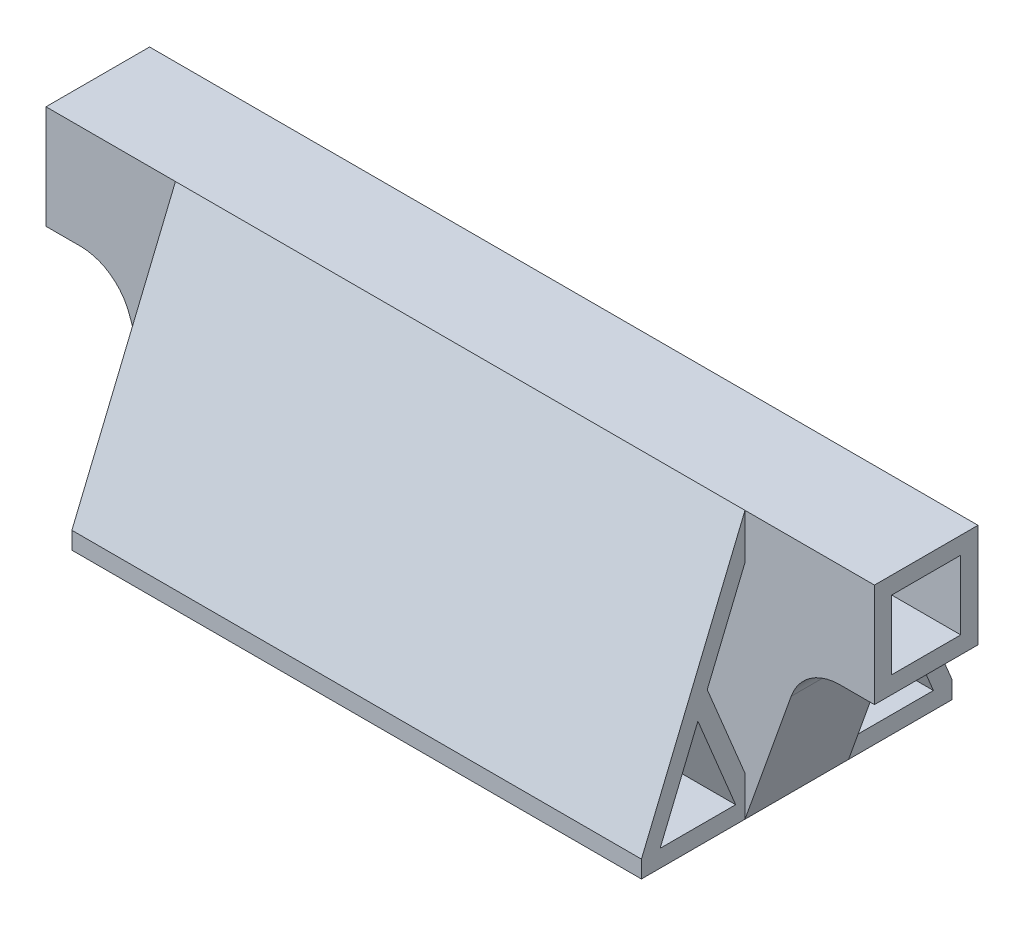
SolidWorks part; units mm, degrees
ref_plane "Front" through (0, 0, 0) normal (0, 0, 1) x (1, 0, 0)
ref_plane "Top" through (0, 0, 0) normal (0, 1, 0) x (1, 0, 0)
ref_plane "Right" through (0, 0, 0) normal (1, 0, 0) x (0, 0, -1)
sketch "Sketch1" plane through (0, 0, 0) normal (0, 0, 1) x (1, 0, 0)
  line L0 (-52.3875, 0) -> (52.3875, 0)
  line L1 (-52.3875, 0) -> (-52.3875, 30.1625) construction
  line L2 (52.3875, 0) -> (52.3875, 30.1625) construction
  line L3 (-52.3875, 30.1625) -> (52.3875, 30.1625) construction
  line L4 (-52.3875, 30.1625) -> (-76.2, 30.1625) construction
  line L5 (-76.2, 30.1625) -> (-76.2, 49.2125)
  line L6 (-76.2, 49.2125) -> (76.2, 49.2125)
  line L7 (76.2, 49.2125) -> (76.2, 30.1625)
  line L8 (76.2, 30.1625) -> (52.3875, 30.1625) construction
  line L9 (0, 0) -> (0, 49.2125) construction
  line L10 (-69.85, 20.6375) -> (69.85, 20.6375) construction
  line L11 (-52.3875, 0) -> (-60.8773, 23.8337)
  line L12 (-69.85, 30.1625) -> (-76.2, 30.1625)
  line L13 (52.3875, 0) -> (60.8773, 23.8337)
  line L14 (69.85, 30.1625) -> (76.2, 30.1625)
  circle A0 centre (-69.85, 20.6375) radius 9.525 construction
  circle A1 centre (69.85, 20.6375) radius 9.525 construction
  arc A2 (-60.8773, 23.8337) -> (-69.85, 30.1625) centre (-69.85, 20.6375) ccw
  arc A3 (60.8773, 23.8337) -> (69.85, 30.1625) centre (69.85, 20.6375) cw
  point P15 (0, 20.6375)
  dimension "D6" = 19.05
  dimension "D1" = 104.775
  dimension "D2" = 30.1625
  dimension "D3" = 152.4
  dimension "D4" = 19.05
  dimension "D5" = 17.4625
extrude "Boss-Extrude1" add sketch "Sketch1" along normal mid plane 57.15
sketch "Sketch11" plane through (0, 0, 0) normal (1, 0, 0) x (0, 0, -1)
  line L0 (-28.575, 0) -> (-28.575, 3.175) construction
  line L1 (-28.575, 0) -> (-28.575, 23.8337) construction
  line L2 (-28.575, 3.175) -> (28.575, 3.175) construction
  line L3 (28.575, 0) -> (28.575, 23.8337) construction
  line L4 (28.575, 3.175) -> (28.575, 0) construction
  line L5 (-9.525, 49.2125) -> (-9.525, 30.1625) construction
  line L6 (-28.575, 49.2125) -> (28.575, 49.2125) construction
  line L7 (-9.525, 30.1625) -> (9.525, 30.1625) construction
  line L8 (9.525, 30.1625) -> (9.525, 49.2125) construction
  line L9 (9.525, 49.2125) -> (-9.525, 49.2125) construction
  line L10 (0, 0) -> (0, 30.1625) construction
  line L11 (-28.575, 0) -> (28.575, 0) construction
  line L12 (-9.525, 30.1625) -> (-28.575, 3.175)
  line L13 (-28.575, 3.175) -> (-28.575, 49.2125)
  line L14 (-28.575, 49.2125) -> (-9.525, 49.2125)
  line L15 (-9.525, 49.2125) -> (-9.525, 30.1625)
  line L16 (28.575, 3.175) -> (9.525, 30.1625)
  line L17 (9.525, 30.1625) -> (9.525, 49.2125)
  line L18 (9.525, 49.2125) -> (28.575, 49.2125)
  line L19 (28.575, 49.2125) -> (28.575, 3.175)
  line L20 (0, 46.0375) -> (0, 49.2125) construction
  line L21 (-6.35, 33.3375) -> (6.35, 33.3375)
  line L22 (-6.35, 33.3375) -> (-6.35, 46.0375)
  line L23 (-6.35, 46.0375) -> (6.35, 46.0375)
  line L24 (6.35, 33.3375) -> (6.35, 46.0375)
  line L25 (-6.35, 33.3375) -> (6.35, 46.0375) construction
  line L26 (-6.35, 46.0375) -> (6.35, 33.3375) construction
  line L27 (6.35, 39.6875) -> (9.525, 39.6875) construction
  line L28 (-6.35, 39.6875) -> (-9.525, 39.6875) construction
  line L29 (0, 33.3375) -> (0, 30.1625) construction
  line L30 (-9.525, 30.1625) -> (-9.525, 3.175) construction
  line L31 (9.525, 30.1625) -> (9.525, 3.175) construction
  line L32 (-24.6887, 3.175) -> (-12.7, 20.159)
  line L33 (-12.7, 20.159) -> (-12.7, 3.175)
  line L34 (-12.7, 3.175) -> (-24.6887, 3.175)
  line L36 (-12.7, 11.667) -> (-9.525, 11.667) construction
  line L37 (-18.6943, 11.667) -> (-21.2882, 13.4979) construction
  line L38 (24.6887, 3.175) -> (12.7, 3.175)
  line L39 (12.7, 3.175) -> (12.7, 20.159)
  line L40 (12.7, 20.159) -> (24.6887, 3.175)
  line L41 (18.6943, 11.667) -> (21.2882, 13.4979) construction
  line L43 (12.7, 11.667) -> (9.525, 11.667) construction
  point P23 (0, 39.6875)
  point P40 (13.3372, 18.1514)
  dimension "D1" = 19.05
  dimension "D2" = 3.175
  dimension "D3" = 12.7
extrude "Cut-Extrude8" [suppressed] cut sketch "Sketch11" against normal through all both and the other way through all
sketch "Sketch2" plane through (0, 0, 0) normal (0, 0, 1) x (1, 0, 0)
  line L8 (-69.85, 33.3375) -> (69.85, 33.3375)
  line L9 (-61.4497, 30.1625) -> (-1.5875, 30.1625)
  line L11 (69.85, 30.1625) -> (76.2, 30.1625) construction
  line L12 (0, 30.1625) -> (0, 33.3375) construction
  line L13 (0, 30.1625) -> (0, 3.175) construction
  line L14 (1.5875, 3.175) -> (1.5875, 30.1625)
  line L15 (-1.5875, 30.1625) -> (-1.5875, 3.175)
  line L16 (-57.8863, 24.8991) -> (-50.148, 3.175)
  line L17 (-50.148, 3.175) -> (50.148, 3.175)
  line L18 (-57.8863, 24.8991) -> (-50.148, 3.175)
  line L19 (50.148, 3.175) -> (57.8863, 24.8991)
  line L20 (73.025, 33.3375) -> (73.025, 46.0375)
  line L21 (73.025, 46.0375) -> (-73.025, 46.0375)
  line L22 (-73.025, 46.0375) -> (-73.025, 33.3375)
  line L23 (50.148, 3.175) -> (57.8863, 24.8991)
  line L25 (-50.148, 3.175) -> (-1.5875, 3.175)
  line L28 (73.025, 33.3375) -> (73.025, 46.0375)
  line L29 (73.025, 46.0375) -> (-73.025, 46.0375)
  line L30 (-73.025, 46.0375) -> (-73.025, 33.3375)
  line L32 (1.5875, 16.6687) -> (-1.5875, 16.6687) construction
  line L33 (0, 3.175) -> (0, 0) construction
  line L34 (1.5875, 3.175) -> (50.148, 3.175)
  line L35 (69.85, 33.3375) -> (73.025, 33.3375)
  line L36 (69.85, 33.3375) -> (73.025, 33.3375)
  line L37 (-73.025, 33.3375) -> (-69.85, 33.3375)
  line L38 (-73.025, 33.3375) -> (-69.85, 33.3375)
  line L39 (1.5875, 30.1625) -> (61.4497, 30.1625)
  line L40 (1.5875, 30.1625) -> (0, 30.1625) construction
  line L41 (0, 30.1625) -> (-1.5875, 30.1625) construction
  line L42 (1.5875, 3.175) -> (0, 3.175) construction
  line L43 (0, 3.175) -> (-1.5875, 3.175) construction
  arc A2 (69.85, 33.3375) -> (57.8863, 24.8991) centre (69.85, 20.6375) ccw
  arc A3 (61.4497, 30.1625) -> (57.8863, 24.8991) centre (69.85, 20.6375) ccw
  arc A4 (-57.8863, 24.8991) -> (-69.85, 33.3375) centre (-69.85, 20.6375) ccw
  arc A5 (-57.8863, 24.8991) -> (-61.4497, 30.1625) centre (-69.85, 20.6375) ccw
  dimension "D1" = 3.175
extrude "Cut-Extrude1" cut sketch "Sketch2" along normal offset from surface 22.225 and the other way offset from surface (6.35 mm away) 22.225 up to face at (0, 26.9588, 28.575) other way up to face at (0, 26.9588, -28.575)
sketch "Sketch3" plane through (0, 0, 0) normal (1, 0, 0) x (0, 0, -1)
  line L0 (0, 0) -> (0, 39.6875) construction
  line L1 (-6.35, 33.3375) -> (6.35, 33.3375)
  line L2 (-6.35, 33.3375) -> (-6.35, 46.0375)
  line L3 (-6.35, 46.0375) -> (6.35, 46.0375)
  line L4 (6.35, 33.3375) -> (6.35, 46.0375)
  line L5 (-6.35, 33.3375) -> (6.35, 46.0375) construction
  line L6 (-6.35, 46.0375) -> (6.35, 33.3375) construction
  line L7 (-28.575, 0) -> (28.575, 0) construction
  line L8 (0, 39.6875) -> (28.575, 39.6875) construction
  line L9 (28.575, 30.1625) -> (28.575, 49.2125) construction
  point P0 (0, 39.6875)
  dimension "D1" = 12.7
extrude "Cut-Extrude2" cut sketch "Sketch3" against normal through all both and the other way through all
sketch "Sketch6" plane through (0, 0, 0) normal (1, 0, 0) x (0, 0, -1)
  line L1 (28.575, 49.2125) -> (9.525, 49.2125)
  line L2 (-28.575, 49.2125) -> (28.575, 49.2125) construction
  line L4 (-9.525, 49.2125) -> (-9.525, 30.1625) construction
  line L5 (-28.575, 30.1625) -> (28.575, 30.1625) construction
  line L6 (-9.525, 30.1625) -> (9.525, 30.1625) construction
  line L7 (9.525, 30.1625) -> (9.525, 49.2125) construction
  line L8 (9.525, 49.2125) -> (-9.525, 49.2125) construction
  line L9 (6.35, 39.6875) -> (9.525, 39.6875) construction
  line L10 (6.35, 33.3375) -> (6.35, 46.0375) construction
  line L11 (-9.525, 39.6875) -> (-6.35, 39.6875) construction
  line L12 (-6.35, 46.0375) -> (-6.35, 33.3375) construction
  line L13 (9.525, 30.1625) -> (9.525, 7.3269) construction
  line L14 (-28.575, 0) -> (28.575, 0) construction
  line L15 (11.243, 3.175) -> (28.575, 3.175) construction
  line L16 (-9.525, 30.1625) -> (-9.525, 7.3269) construction
  line L17 (9.525, 3.175) -> (-9.525, 3.175) construction
  line L18 (-11.243, 3.175) -> (-28.575, 3.175) construction
  line L19 (-28.575, 0) -> (-28.575, 23.8337) construction
  line L20 (0, 3.175) -> (0, 0) construction
  line L21 (9.525, 40.9086) -> (9.525, 7.3269)
  line L22 (11.243, 3.175) -> (25.1389, 3.175)
  line L23 (25.1389, 3.175) -> (18.191, 19.9658)
  line L24 (17.332, 22.0418) -> (20.2657, 23.2558) construction
  line L25 (-9.525, 49.2125) -> (-28.575, 3.175)
  line L26 (-28.575, 3.175) -> (-28.575, 49.2125)
  line L27 (-28.575, 49.2125) -> (-9.525, 49.2125)
  line L28 (-25.1389, 3.175) -> (-11.243, 3.175)
  line L29 (-9.525, 7.3269) -> (-9.525, 40.9086)
  line L30 (-9.525, 40.9086) -> (-16.4729, 24.1178)
  line L31 (-17.332, 22.0418) -> (-20.2657, 23.2558) construction
  line L32 (-9.525, 3.175) -> (-17.332, 22.0418) construction
  line L33 (9.525, 3.175) -> (17.332, 22.0418) construction
  line L34 (-9.525, 7.3269) -> (-16.4729, 24.1178)
  line L35 (-11.243, 3.175) -> (-18.191, 19.9658)
  line L36 (-14.717, 11.5704) -> (-11.7833, 12.7844) construction
  line L37 (9.525, 7.3269) -> (16.4729, 24.1178)
  line L38 (11.243, 3.175) -> (18.191, 19.9658)
  line L39 (14.717, 11.5704) -> (11.7833, 12.7844) construction
  line L40 (-18.191, 19.9658) -> (-25.1389, 3.175)
  line L41 (-9.525, 3.175) -> (-9.525, 0) construction
  line L42 (9.525, 3.175) -> (9.525, 0) construction
  line L43 (16.4729, 24.1178) -> (9.525, 40.9086)
  line L44 (-11.243, 3.175) -> (-9.525, 3.175) construction
  line L45 (-9.525, 3.175) -> (-9.525, 7.3269) construction
  line L46 (-18.191, 19.9658) -> (-17.332, 22.0418) construction
  line L47 (-17.332, 22.0418) -> (-16.4729, 24.1178) construction
  line L48 (9.525, 7.3269) -> (9.525, 3.175) construction
  line L49 (9.525, 3.175) -> (11.243, 3.175) construction
  line L50 (18.191, 19.9658) -> (17.332, 22.0418) construction
  line L51 (17.332, 22.0418) -> (16.4729, 24.1178) construction
  line L52 (28.575, 0) -> (28.575, 23.8337) construction
  line L53 (28.575, 3.175) -> (28.575, 49.2125)
  line L54 (9.525, 49.2125) -> (28.575, 3.175)
  dimension "D1" = 3.175
extrude "Cut-Extrude4" cut sketch "Sketch6" against normal through all both and the other way through all
sketch "Sketch8" plane through (0, 0, 0) normal (0, -1, 0) x (1, 0, 0)
  line L1 (52.3875, 28.575) -> (76.2, 28.575)
  line L2 (52.3875, 28.575) -> (52.3875, 9.525)
  line L3 (52.3875, 9.525) -> (76.2, 9.525)
  line L4 (76.2, 28.575) -> (76.2, 9.525)
  line L5 (52.3875, -28.575) -> (76.2, -28.575)
  line L6 (52.3875, -28.575) -> (52.3875, -9.525)
  line L7 (52.3875, -9.525) -> (76.2, -9.525)
  line L8 (76.2, -28.575) -> (76.2, -9.525)
  line L9 (-52.3875, 28.575) -> (-76.2, 28.575)
  line L10 (-52.3875, 28.575) -> (-52.3875, 9.525)
  line L11 (-52.3875, 9.525) -> (-76.2, 9.525)
  line L12 (-76.2, 28.575) -> (-76.2, 9.525)
  line L13 (-52.3875, -28.575) -> (-76.2, -28.575)
  line L14 (-52.3875, -28.575) -> (-52.3875, -9.525)
  line L15 (-52.3875, -9.525) -> (-76.2, -9.525)
  line L16 (-76.2, -28.575) -> (-76.2, -9.525)
extrude "Cut-Extrude5" cut sketch "Sketch8" against normal through all
sketch "Sketch9" plane through (0, 10.5597, -25.5193) normal (0, 0.3824, -0.924) x (-1, 0, 0)
  line L0 (0, -6.6782) -> (0, 11.4934) construction
  line L1 (0, 15.9868) -> (0, 34.1584) construction
  line L2 (-1.5875, -6.6782) -> (-1.5875, 11.4934) construction
  line L3 (-1.5875, 15.9868) -> (-1.5875, 34.1584) construction
  line L4 (-52.3875, 15.9868) -> (52.3875, 15.9868)
  line L5 (-52.3875, 34.1584) -> (-52.3875, 15.9868)
  line L6 (52.3875, 34.1584) -> (-52.3875, 34.1584)
  line L7 (-52.3875, 34.1584) -> (-52.3875, 15.9868) construction
  line L8 (-52.3875, 15.9868) -> (52.3875, 15.9868) construction
  line L10 (52.3875, 34.1584) -> (-52.3875, 34.1584) construction
  line L12 (-52.3875, -6.6782) -> (52.3875, -6.6782)
  line L13 (-52.3875, 11.4934) -> (-52.3875, -6.6782)
  line L14 (52.3875, 11.4934) -> (-52.3875, 11.4934)
  line L15 (-52.3875, 11.4934) -> (-52.3875, -6.6782) construction
  line L16 (-52.3875, -6.6782) -> (52.3875, -6.6782) construction
  line L18 (52.3875, 11.4934) -> (-52.3875, 11.4934) construction
  line L20 (1.5875, -6.6782) -> (1.5875, 11.4934) construction
  line L21 (1.5875, 15.9868) -> (1.5875, 34.1584) construction
  line L22 (-1.5875, 2.4076) -> (1.5875, 2.4076) construction
  line L23 (-1.5875, 25.0726) -> (1.5875, 25.0726) construction
  line L24 (-49.2125, 34.1584) -> (-49.2125, 15.9868) construction
  line L25 (-49.2125, 11.4934) -> (-49.2125, -6.6782) construction
  line L26 (49.2125, 34.1584) -> (49.2125, 15.9868) construction
  line L27 (49.2125, 11.4934) -> (49.2125, -6.6782) construction
  line L28 (49.2125, 2.4076) -> (52.3875, 2.4076) construction
  line L29 (49.2125, 25.0726) -> (52.3875, 25.0726) construction
  line L30 (-52.3875, 25.0726) -> (-49.2125, 25.0726) construction
  line L31 (-52.3875, 2.4076) -> (-49.2125, 2.4076) construction
  line L47 (-47.625, 9.9059) -> (-3.175, 9.9059) construction
  line L48 (-3.175, 9.9059) -> (-3.175, -5.0907) construction
  line L49 (-3.175, -5.0907) -> (-47.625, -5.0907) construction
  line L50 (-47.625, -5.0907) -> (-47.625, 9.9059) construction
  line L66 (-49.2125, 2.4076) -> (-47.625, 2.4076) construction
  line L67 (-3.175, 2.4076) -> (-1.5875, 2.4076) construction
  line L68 (-25.4, -5.0907) -> (-25.4, -6.6782) construction
  line L69 (-25.4, 9.9059) -> (-25.4, 11.4934) construction
  line L85 (-47.625, -5.0907) -> (-47.625, 3.8568)
  line L86 (-47.625, 3.8568) -> (-42.1077, -5.0907)
  line L87 (-42.1077, -5.0907) -> (-47.625, -5.0907)
  line L88 (-47.625, 9.9059) -> (-38.3776, -5.0907)
  line L104 (-38.3776, -5.0907) -> (-29.1301, 9.9059)
  line L105 (-29.1301, 9.9059) -> (-47.625, 9.9059)
  line L106 (-34.6474, -5.0907) -> (-25.4, 9.9059)
  line L107 (-25.4, 9.9059) -> (-16.1526, -5.0907)
  line L108 (52.3875, -7.9919) -> (52.3875, 41.8313) construction
  line L109 (-16.1526, -5.0907) -> (-34.6474, -5.0907)
  line L110 (-3.175, 9.9059) -> (-12.4224, -5.0907)
  line L111 (-12.4224, -5.0907) -> (-21.6699, 9.9059)
  line L112 (52.3875, -6.6782) -> (52.3875, 11.4934)
  line L113 (52.3875, -6.6782) -> (52.3875, 11.4934) construction
  line L114 (52.3875, 15.9868) -> (52.3875, 34.1584)
  line L115 (52.3875, 15.9868) -> (52.3875, 34.1584) construction
  line L116 (-21.6699, 9.9059) -> (-3.175, 9.9059)
  line L117 (-3.175, -5.0907) -> (-3.175, 3.8568)
  line L118 (-3.175, 3.8568) -> (-8.6923, -5.0907)
  line L119 (-8.6923, -5.0907) -> (-3.175, -5.0907)
  line L120 (-5.9337, -0.6169) -> (-8.6362, 1.0495) construction
  line L121 (-17.0462, 2.4076) -> (-19.7487, 0.7412) construction
  line L122 (-33.7538, 2.4076) -> (-31.0513, 0.7412) construction
  line L123 (-44.8663, -0.6169) -> (-42.1638, 1.0495) construction
  line L124 (47.625, 3.8568) -> (42.1077, -5.0907)
  line L125 (47.625, -5.0907) -> (47.625, 3.8568)
  line L126 (42.1077, -5.0907) -> (47.625, -5.0907)
  line L127 (38.3776, -5.0907) -> (29.1301, 9.9059)
  line L128 (47.625, 9.9059) -> (38.3776, -5.0907)
  line L129 (29.1301, 9.9059) -> (47.625, 9.9059)
  line L130 (25.4, 9.9059) -> (16.1526, -5.0907)
  line L131 (34.6474, -5.0907) -> (25.4, 9.9059)
  line L132 (16.1526, -5.0907) -> (34.6474, -5.0907)
  line L133 (12.4224, -5.0907) -> (21.6699, 9.9059)
  line L134 (3.175, 9.9059) -> (12.4224, -5.0907)
  line L135 (21.6699, 9.9059) -> (3.175, 9.9059)
  line L136 (3.175, 3.8568) -> (8.6923, -5.0907)
  line L137 (3.175, -5.0907) -> (3.175, 3.8568)
  line L138 (8.6923, -5.0907) -> (3.175, -5.0907)
  line L139 (-52.3875, 13.7401) -> (52.3875, 13.7401) construction
  line L140 (-52.3875, 41.8313) -> (-52.3875, -7.9919) construction
  line L141 (0, 11.4934) -> (0, 15.9868) construction
  line L142 (47.625, 32.5709) -> (47.625, 23.6234)
  line L143 (42.1077, 32.5709) -> (47.625, 32.5709)
  line L144 (47.625, 23.6234) -> (42.1077, 32.5709)
  line L145 (47.625, 17.5743) -> (38.3776, 32.5709)
  line L146 (29.1301, 17.5743) -> (47.625, 17.5743)
  line L147 (38.3776, 32.5709) -> (29.1301, 17.5743)
  line L148 (34.6474, 32.5709) -> (25.4, 17.5743)
  line L149 (16.1526, 32.5709) -> (34.6474, 32.5709)
  line L150 (25.4, 17.5743) -> (16.1526, 32.5709)
  line L151 (3.175, 17.5743) -> (12.4224, 32.5709)
  line L152 (21.6699, 17.5743) -> (3.175, 17.5743)
  line L153 (12.4224, 32.5709) -> (21.6699, 17.5743)
  line L154 (-3.175, 23.6234) -> (-8.6923, 32.5709)
  line L155 (-3.175, 32.5709) -> (-3.175, 23.6234)
  line L156 (-8.6923, 32.5709) -> (-3.175, 32.5709)
  line L157 (3.175, 32.5709) -> (3.175, 23.6234)
  line L158 (8.6923, 32.5709) -> (3.175, 32.5709)
  line L159 (3.175, 23.6234) -> (8.6923, 32.5709)
  line L160 (-12.4224, 32.5709) -> (-21.6699, 17.5743)
  line L161 (-3.175, 17.5743) -> (-12.4224, 32.5709)
  line L162 (-21.6699, 17.5743) -> (-3.175, 17.5743)
  line L163 (-25.4, 17.5743) -> (-16.1526, 32.5709)
  line L164 (-34.6474, 32.5709) -> (-25.4, 17.5743)
  line L165 (-16.1526, 32.5709) -> (-34.6474, 32.5709)
  line L166 (-38.3776, 32.5709) -> (-29.1301, 17.5743)
  line L167 (-47.625, 17.5743) -> (-38.3776, 32.5709)
  line L168 (-29.1301, 17.5743) -> (-47.625, 17.5743)
  line L169 (-47.625, 23.6234) -> (-42.1077, 32.5709)
  line L170 (-47.625, 32.5709) -> (-47.625, 23.6234)
  line L171 (-42.1077, 32.5709) -> (-47.625, 32.5709)
  point P87 (0, 13.7401)
  dimension "D3" = 3.175
  dimension "D4" = 1.5875
  dimension "D1" = 0
  dimension "D2" = 0
extrude "Cut-Extrude7" cut sketch "Sketch9" against normal up to next
sketch "Sketch16" plane through (0, -2.294, -5.5439) normal (0, 0.3824, 0.924) x (1, 0, 0)
  line L0 (-49.2125, 23.8166) -> (-1.5875, 23.8166)
  line L1 (0, 7.2326) -> (0, 25.4041) construction
  line L2 (-1.5875, 23.8166) -> (-1.5875, 8.8201)
  line L3 (-1.5875, 8.8201) -> (-49.2125, 8.8201)
  line L4 (52.3875, 25.4041) -> (-52.3875, 25.4041)
  line L5 (52.3875, 7.2326) -> (52.3875, 25.4041)
  line L6 (-52.3875, 7.2326) -> (52.3875, 7.2326)
  line L7 (-52.3875, 25.4041) -> (-52.3875, 7.2326)
  line L8 (52.3875, 25.4041) -> (-52.3875, 25.4041) construction
  line L9 (52.3875, 7.2326) -> (52.3875, 25.4041) construction
  line L10 (-52.3875, 7.2326) -> (52.3875, 7.2326) construction
  line L11 (-52.3875, 25.4041) -> (-52.3875, 7.2326) construction
  line L12 (-1.5875, 16.3183) -> (1.5875, 16.3183) construction
  line L13 (-49.2125, 8.8201) -> (-49.2125, 23.8166)
  line L14 (1.5875, 23.8166) -> (49.2125, 23.8166)
  line L15 (49.2125, 23.8166) -> (49.2125, 8.8201)
  line L16 (49.2125, 8.8201) -> (1.5875, 8.8201)
  line L17 (1.5875, 8.8201) -> (1.5875, 23.8166)
  line L18 (49.2125, 16.3183) -> (52.3875, 16.3183) construction
  line L19 (-49.2125, 16.3183) -> (-52.3875, 16.3183) construction
  line L20 (-25.4, 23.8166) -> (-25.4, 25.4041) construction
  line L21 (-25.4, 8.8201) -> (-25.4, 7.2326) construction
  line L22 (25.4, 8.8201) -> (25.4, 7.2326) construction
  line L23 (25.4, 23.8166) -> (25.4, 25.4041) construction
  point P20 (0, 16.3183)
  dimension "D2" = 3.175
  dimension "D3" = 1.5875
  dimension "D1" = 0
extrude "Cut-Extrude11" cut sketch "Sketch16" against normal up to next
fillet "Fillet9" radius 1.5875 24 edges at (-47.625, 31.7811, -15.0199) (-42.1077, 40.0487, -11.5989) (-47.625, 40.0487, -11.5989) (-42.1077, 5.2489, -25.9988) (-47.625, 13.5165, -22.5777) (-47.625, 5.2489, -25.9988) (-3.175, 31.7811, -15.0199) (-8.6923, 40.0487, -11.5989) (-3.175, 40.0487, -11.5989) (3.175, 31.7811, -15.0199) (8.6923, 40.0487, -11.5989) (3.175, 40.0487, -11.5989) (-8.6923, 5.2489, -25.9988) (-3.175, 5.2489, -25.9988) (-3.175, 13.5165, -22.5777) (3.175, 13.5165, -22.5777) (8.6923, 5.2489, -25.9988) (3.175, 5.2489, -25.9988) (42.1077, 5.2489, -25.9988) (47.625, 5.2489, -25.9988) (47.625, 13.5165, -22.5777) (42.1077, 40.0487, -11.5989) (47.625, 31.7811, -15.0199) (47.625, 40.0487, -11.5989)
fillet "Fillet10" radius 3.175 36 edges at (38.3776, 5.2489, -25.9988) (29.1301, 19.106, -20.2648) (47.625, 19.106, -20.2648) (29.1301, 26.1916, -17.3328) (38.3776, 40.0487, -11.5989) (16.1526, 40.0487, -11.5989) (34.6474, 40.0487, -11.5989) (25.4, 26.1916, -17.3328) (34.6474, 5.2489, -25.9988) (16.1526, 5.2489, -25.9988) (25.4, 19.106, -20.2648) (12.4224, 5.2489, -25.9988) (3.175, 19.106, -20.2648) (21.6699, 19.106, -20.2648) (-16.1526, 5.2489, -25.9988) (-34.6474, 5.2489, -25.9988) (-25.4, 19.106, -20.2648) (-21.6699, 19.106, -20.2648) (-3.175, 19.106, -20.2648) (-12.4224, 5.2489, -25.9988) (-29.1301, 19.106, -20.2648) (-38.3776, 5.2489, -25.9988) (-47.625, 19.106, -20.2648) (-12.4224, 40.0487, -11.5989) (-3.175, 26.1916, -17.3328) (-21.6699, 26.1916, -17.3328) (21.6699, 26.1916, -17.3328) (3.175, 26.1916, -17.3328) (12.4224, 40.0487, -11.5989) (-25.4, 26.1916, -17.3328) (-34.6474, 40.0487, -11.5989) (-16.1526, 40.0487, -11.5989) (-38.3776, 40.0487, -11.5989) (-29.1301, 26.1916, -17.3328) (-47.625, 26.1916, -17.3328) (47.625, 26.1916, -17.3328)
